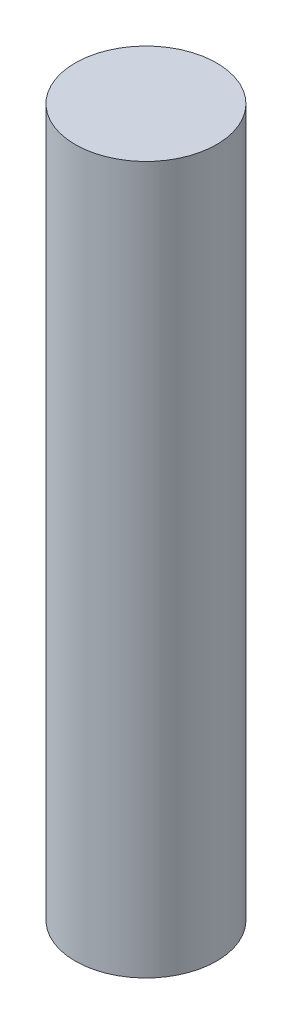
SolidWorks part; units mm, degrees
ref_plane "Front Plane" through (0, 0, 0) normal (0, 0, 1) x (1, 0, 0)
ref_plane "Top Plane" through (0, 0, 0) normal (0, 1, 0) x (1, 0, 0)
ref_plane "Right Plane" through (0, 0, 0) normal (1, 0, 0) x (0, 0, -1)
sketch "Sketch1" plane through (0, 0, 0) normal (0, 1, 0) x (1, 0, 0)
  circle A0 centre (0, 0) radius 0.7937
  dimension "D1" = 1.5875
extrude "Boss-Extrude1" add sketch "Sketch1" along normal blind 7.9375
